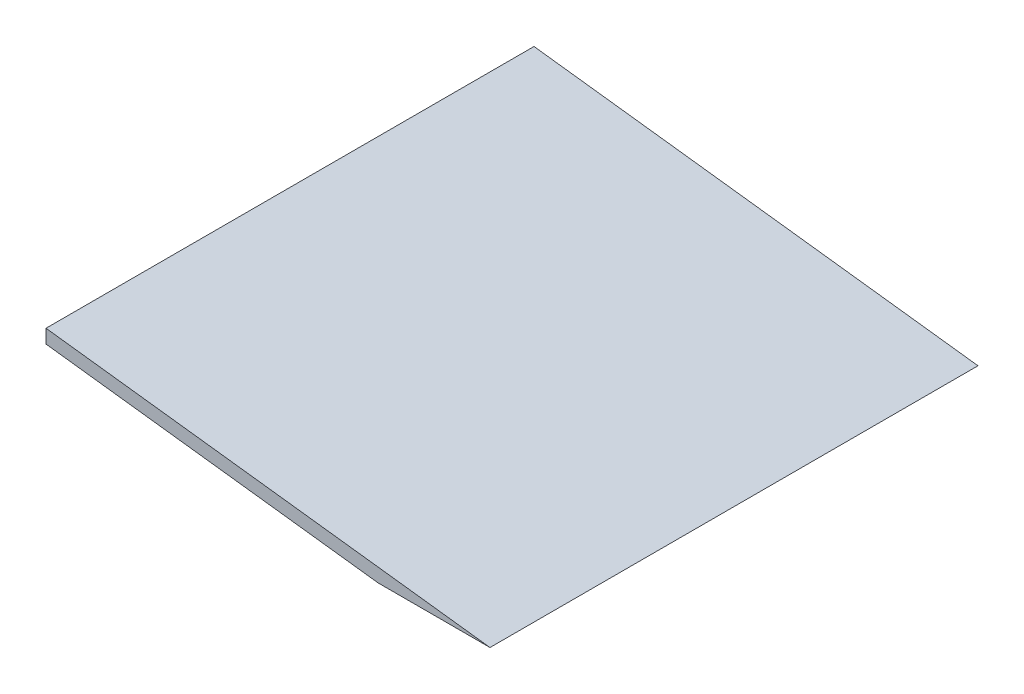
SolidWorks part; units mm, degrees
ref_plane "Front Plane" through (0, 0, 0) normal (0, 0, 1) x (1, 0, 0)
ref_plane "Top Plane" through (0, 0, 0) normal (0, 1, 0) x (1, 0, 0)
ref_plane "Right Plane" through (0, 0, 0) normal (1, 0, 0) x (0, 0, -1)
sketch "Sketch1" plane through (0, 0, 0) normal (0, 0, 1) x (1, 0, 0)
  line L0 (0, 0) -> (103.4332, -12.7)
  line L1 (103.4332, -12.7) -> (77.3807, -12.7)
  line L2 (77.3807, -12.7) -> (0, -3.1988)
  line L3 (0, -3.1988) -> (0, 0)
  dimension "D1" = 12.7
  dimension "D2" = 3.175
  dimension "D3" = 7
  dimension "D4" = 103.4332
  dimension "D5" = 83
extrude "Boss-Extrude1" add sketch "Sketch1" along normal blind 113.6904
